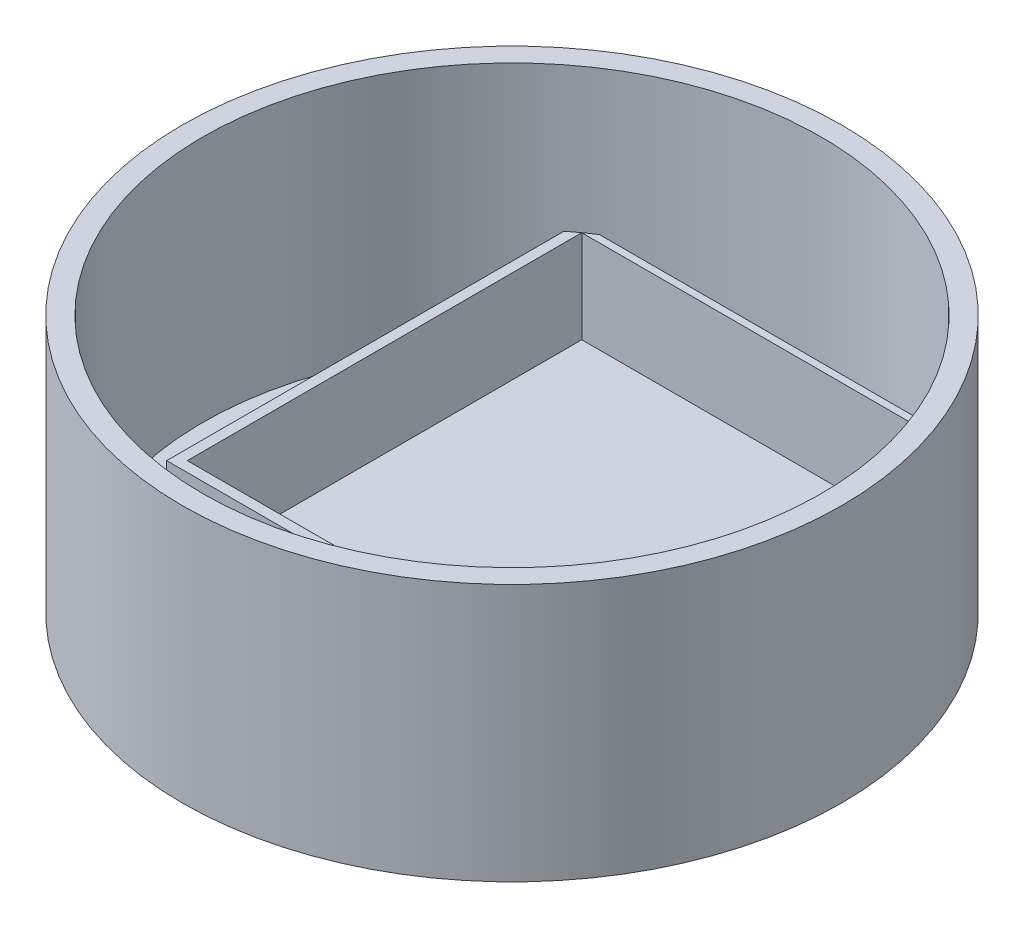
SolidWorks part; units mm, degrees
ref_plane "Front Plane" through (0, 0, 0) normal (0, 0, 1) x (1, 0, 0)
ref_plane "Top Plane" through (0, 0, 0) normal (0, 1, 0) x (1, 0, 0)
ref_plane "Right Plane" through (0, 0, 0) normal (1, 0, 0) x (0, 0, -1)
sketch "Sketch2" plane through (0, 0, 0) normal (0, 1, 0) x (1, 0, 0)
  circle A1 centre (0, 0) radius 32
extrude "Boss-Extrude1" add sketch "Sketch2" along normal blind 25
sketch "Sketch3" plane through (0, 25, 0) normal (0, 1, 0) x (1, 0, 0)
  circle A0 centre (0, 0) radius 30
extrude "Cut-Extrude1" cut sketch "Sketch3" against normal blind 24
sketch "Sketch4" plane through (0, 1, 0) normal (0, 1, 0) x (1, 0, 0)
  line L0 (0, 0) -> (0, 30) construction
  line L4 (-18.5412, -14.9722) -> (18.5412, -14.975)
  line L5 (16.5412, 25.0278) -> (-16.5412, 25.0278)
  line L6 (18.5412, 23.5844) -> (18.5412, -14.975)
  line L9 (-18.5412, -14.9722) -> (-18.5412, 23.5844)
  circle A0 centre (0, 0) radius 30 construction
  arc A1 (16.5412, 25.0278) -> (18.5412, 23.5844) centre (0, 0) cw
  arc A2 (-18.5412, 23.5844) -> (-16.5412, 25.0278) centre (0, 0) cw
extrude "Boss-Extrude2" add sketch "Sketch4" along normal blind 10
sketch "Sketch5" plane through (0, 11, 0) normal (0, 1, 0) x (1, 0, 0)
  line L0 (0, -14.9736) -> (0, -13.9736) construction
  line L1 (-18.5412, -14.9722) -> (18.5412, -14.975) construction
  line L2 (-17.5412, -13.9736) -> (17.5412, -13.9736)
  line L3 (18.5412, -14.975) -> (18.5412, 23.5844) construction
  line L4 (0, 25.0278) -> (0, 24.0278) construction
  line L5 (16.5412, 25.0278) -> (-16.5412, 25.0278) construction
  line L6 (17.5412, -13.9736) -> (17.556, 24.3266)
  line L7 (17.556, 24.3266) -> (-17.556, 24.3266)
  line L8 (-17.556, 24.3266) -> (-17.5412, -13.9736)
  arc A0 (18.5412, 23.5844) -> (16.5412, 25.0278) centre (0, 0) ccw construction
  arc A1 (-16.5412, 25.0278) -> (-18.5412, 23.5844) centre (0, 0) ccw construction
  point P8 (0, -13.9736)
  dimension "D1" = 1
  dimension "D2" = 1
  dimension "D3" = 1
extrude "Cut-Extrude2" cut sketch "Sketch5" against normal blind 9
